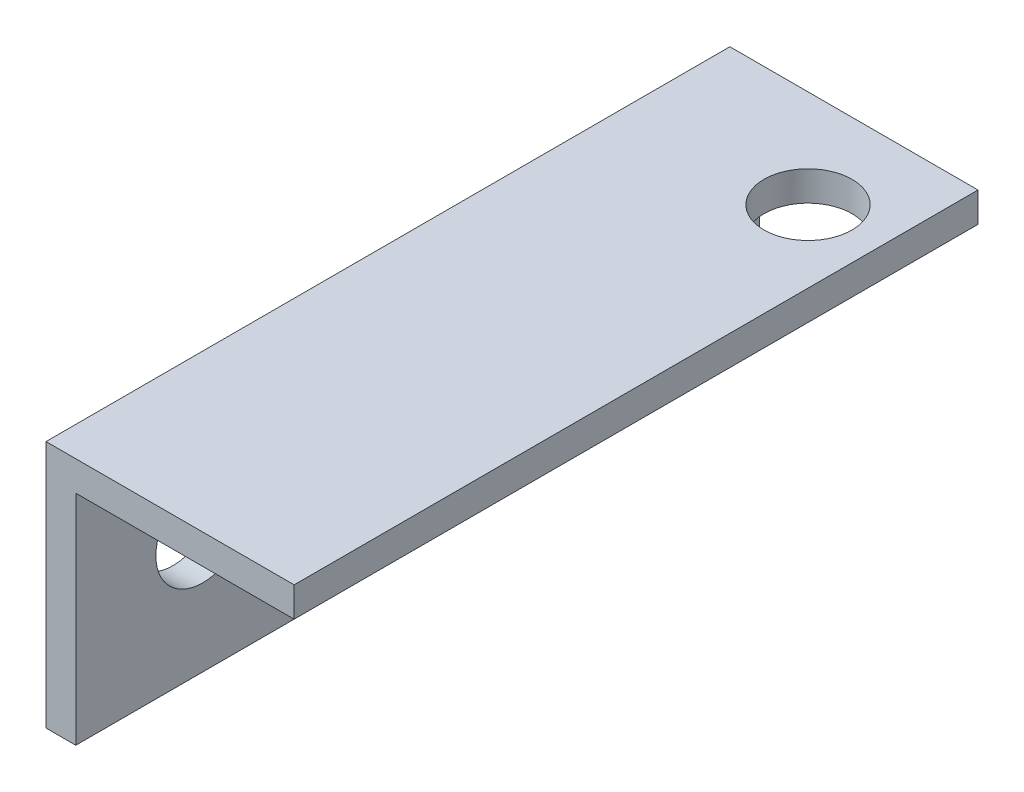
SolidWorks part; units mm, degrees
ref_plane "Front Plane" through (0, 0, 0) normal (0, 0, 1) x (1, 0, 0)
ref_plane "Top Plane" through (0, 0, 0) normal (0, 1, 0) x (1, 0, 0)
ref_plane "Right Plane" through (0, 0, 0) normal (1, 0, 0) x (0, 0, -1)
sketch "Sketch1" plane through (0, 0, 0) normal (0, 0, 1) x (1, 0, 0)
  line L0 (0, 0) -> (12.7, 0)
  line L1 (12.7, 0) -> (12.7, -1.524)
  line L2 (12.7, -1.524) -> (1.524, -1.524)
  line L3 (1.524, -1.524) -> (1.524, -12.7)
  line L4 (1.524, -12.7) -> (0, -12.7)
  line L5 (0, -12.7) -> (0, 0)
  dimension "D1" = 12.7
  dimension "D2" = 1.524
extrude "Boss-Extrude1" add sketch "Sketch1" along normal blind 35
hole_wizard "M4 Clearance Hole1" positions "Sketch2" profile "Sketch3" hole size "M4" standard "ANSI Metric" end condition through all
sketch "Sketch2" plane through (0, 0, 0) normal (0, 1, 0) x (1, 0, 0)
  line L0 (9, -5) -> (9, 0) construction
  line L3 (12.7, 0) -> (0, 0) construction
  point P2 (9, -5)
  point P12 (0, 0)
  point P15 (0, 0)
  point P16 (9, -15)
  dimension "D1" = 5
  dimension "D3" = 9
sketch "Sketch3" plane through (9, 0, 5) normal (1, 0, 0) x (0, 0, 1)
  line L0 (0, 0) -> (0, 12.7)
  line L1 (0, 12.7) -> (2.25, 12.7)
  line L2 (2.25, 12.7) -> (2.25, 0)
  line L5 (2.25, 0) -> (0, 0)
  line L11 (0, -6.35) -> (0, 107.95) construction
  dimension "Thru Hole Dia." = 4.5
  dimension "Thru Hole Depth" = 12.7
hole_wizard "M4 Clearance Hole2" positions "Sketch4" profile "Sketch5" hole size "M4" standard "ANSI Metric" end condition through all
sketch "Sketch4" plane through (0, 0, 0) normal (-1, 0, 0) x (0, 0, 1)
  line L4 (35, 0) -> (35, -12.7) construction
  line L5 (35, -12.7) -> (0, -12.7) construction
  line L6 (35, -12.7) -> (35, -1.524) construction
  point P10 (15, -6.35)
  point P22 (28.5, -6.35)
  point P27 (0, 0)
  dimension "D1" = 6.35
  dimension "D2" = 6.5
  dimension "D3" = 20
sketch "Sketch5" plane through (0, -6.35, 15) normal (0, 1, 0) x (0, 0, 1)
  line L0 (0, 0) -> (0, 12.7)
  line L1 (0, 12.7) -> (2.4, 12.7)
  line L2 (2.4, 12.7) -> (2.4, 0)
  line L5 (2.4, 0) -> (0, 0)
  line L11 (0, -6.35) -> (0, 107.95) construction
  dimension "Thru Hole Dia." = 4.8
  dimension "Thru Hole Depth" = 12.7
